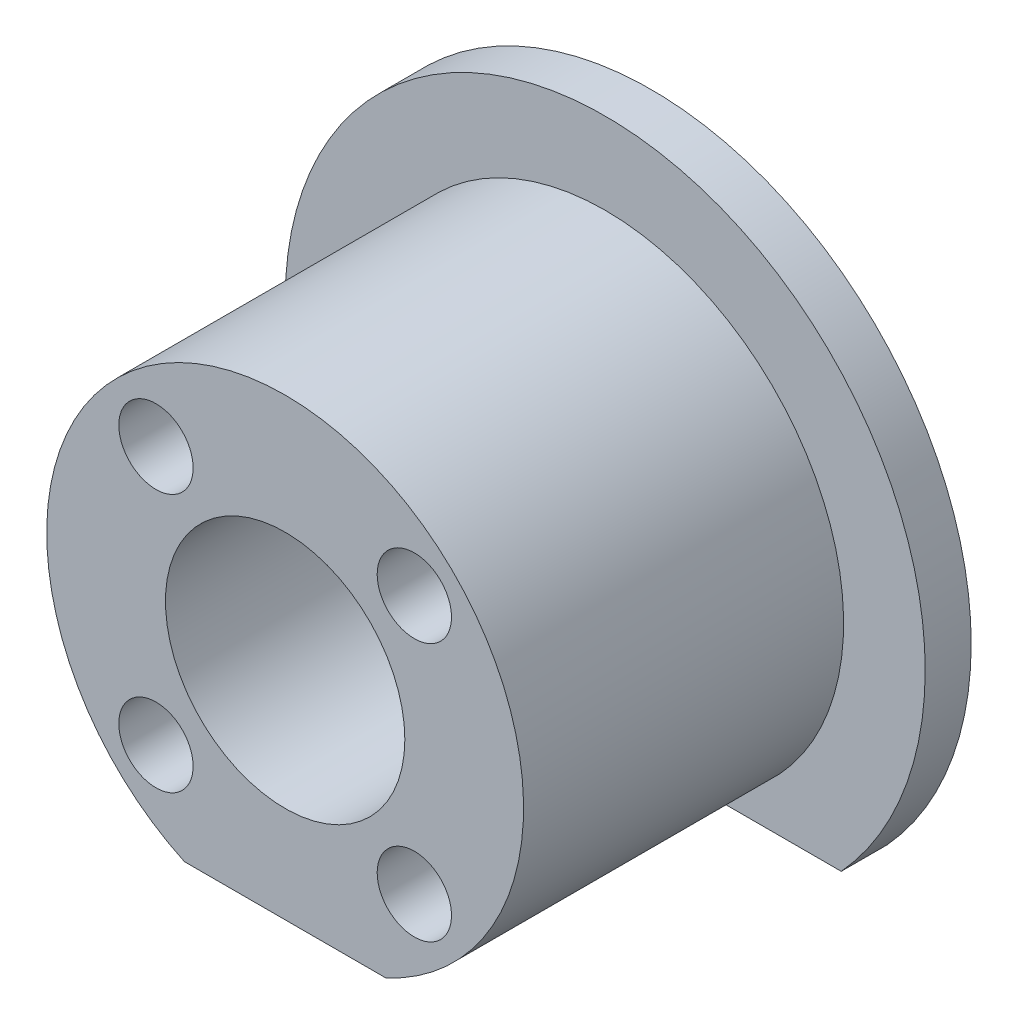
SolidWorks part; units mm, degrees
ref_plane "Front Plane" through (0, 0, 0) normal (0, 0, 1) x (1, 0, 0)
ref_plane "Top Plane" through (0, 0, 0) normal (0, 1, 0) x (1, 0, 0)
ref_plane "Right Plane" through (0, 0, 0) normal (1, 0, 0) x (0, 0, -1)
sketch "Sketch1" plane through (0, 0, 0) normal (0, 0, 1) x (1, 0, 0)
  line L0 (0, 0) -> (0, -18.584) construction
  line L1 (-3.9986, -8.575) -> (3.9986, -8.575)
  line L2 (3.9986, -8.575) -> (46.5083, 11.2476) construction
  arc A0 (-3.9986, -8.575) -> (3.9986, -8.575) centre (0, 0) cw
  circle A1 centre (0, 0) radius 4.75
  point P4 (46.5083, 11.2476)
  dimension "D2" = 9.4615
  dimension "D4" = 9.5
  dimension "D1" = 25
  dimension "D3" = 8.575
extrude "Boss-Extrude1" add sketch "Sketch1" along normal blind 14.525
sketch "Sketch3" plane through (0, 0, 0) normal (0, 0, -1) x (-1, 0, 0)
  line L0 (0, 0) -> (5.1265, -5.1265) construction
  line L1 (3.9986, -8.575) -> (0, 0) construction
  line L2 (0, 0) -> (-3.9986, -8.575) construction
  line L3 (0, 0) -> (0, -13.7827) construction
  circle A0 centre (5.1265, -5.1265) radius 1.475
  circle A1 centre (0, 0) radius 4 construction
  circle A2 centre (5.1265, -5.1265) radius 2.75 construction
  circle A3 centre (-5.1265, -5.1265) radius 1.475
  circle A4 centre (-5.1265, 5.1265) radius 1.475
  circle A5 centre (5.1265, 5.1265) radius 1.475
  point P20 (0, 0)
  dimension "D3" = 2.95
  dimension "D5" = 8
  dimension "D6" = 5.5
  dimension "D1" = 50
  dimension "D2" = 7.25
  dimension "D4" = 45
  dimension "D7" = 4
extrude "Cut-Extrude1" cut sketch "Sketch3" against normal blind 19.05
sketch "Sketch4" plane through (0, 0, 0) normal (0, 0, 1) x (1, 0, 0)
  line L0 (-3.9986, -8.575) -> (3.9986, -8.575) construction
  line L1 (-3.9986, -8.575) -> (3.9986, -8.575) construction
  line L2 (-3.9986, -8.575) -> (-9.368, -8.575)
  line L3 (3.9986, -8.575) -> (9.368, -8.575)
  arc A0 (3.9986, -8.575) -> (-3.9986, -8.575) centre (0, 0) ccw construction
  arc A1 (3.9986, -8.575) -> (-3.9986, -8.575) centre (0, 0) ccw
  arc A2 (-9.368, -8.575) -> (9.368, -8.575) centre (0, 0) cw
  point P6 (7.4792, -8.575)
  dimension "D1" = 12.7
extrude "Boss-Extrude2" add sketch "Sketch4" along normal offset from surface (1.825 mm away) 12.7 up to face at (-6.6015, 5.1265, 14.525)
equation "\"D2@Sketch1\"=0.745/2"
equation "\"D4@Sketch1\"=9.5mm"
equation "\"D2@Sketch3\"=7.25mm"
equation "\"D3@Sketch3\"=2.95mm"
equation "\"D5@Sketch3\"=8mm"
equation "\"D6@Sketch3\"=5.5mm"
equation "\"D1@Boss-Extrude1\"=0.5in+5mm-0.125in"
